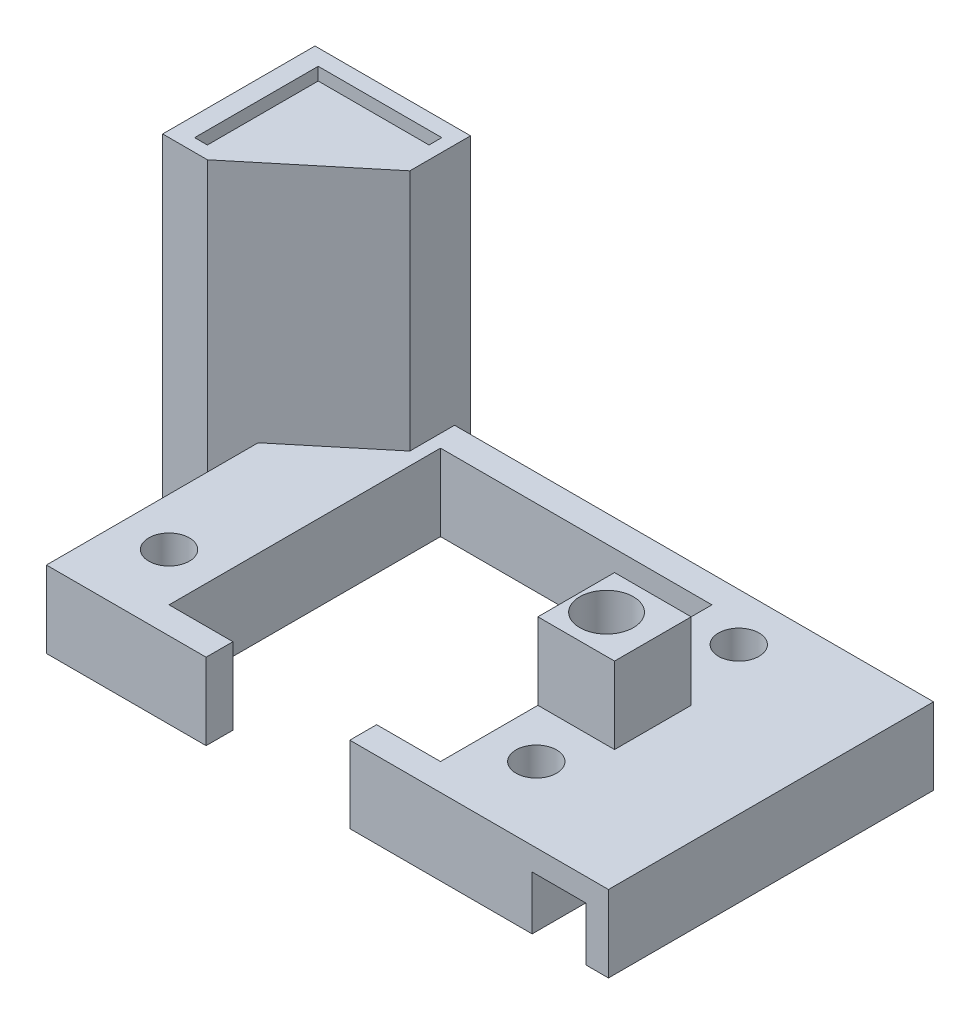
SolidWorks part; units mm, degrees
ref_plane "Front Plane" through (0, 0, 0) normal (0, 0, 1) x (1, 0, 0)
ref_plane "Top Plane" through (0, 0, 0) normal (0, 1, 0) x (1, 0, 0)
ref_plane "Right Plane" through (0, 0, 0) normal (1, 0, 0) x (0, 0, -1)
sketch "Sketch1" plane through (0, 0, 0) normal (0, 1, 0) x (1, 0, 0)
  line L1 (0, 0) -> (42.5, 0)
  line L2 (0, 0) -> (0, 42.5)
  line L3 (0, 42.5) -> (42.5, 42.5)
  line L4 (42.5, 0) -> (42.5, 42.5)
  line L5 (-15, 0) -> (57.5, 0)
  line L6 (-15, 0) -> (-15, 46.7)
  line L7 (-15, 46.7) -> (57.5, 46.7)
  line L8 (57.5, 0) -> (57.5, 46.7)
  line L9 (-15, 0) -> (10, 0)
  line L10 (-15, 0) -> (-15, -4.2)
  line L11 (-15, -4.2) -> (10, -4.2)
  line L12 (10, 0) -> (10, -4.2)
  line L13 (57.5, 0) -> (32.5, 0)
  line L14 (57.5, 0) -> (57.5, -4.2)
  line L15 (57.5, -4.2) -> (32.5, -4.2)
  line L16 (32.5, 0) -> (32.5, -4.2)
  circle A0 centre (-7.5, 7.5) radius 3.175
  circle A2 centre (50, 39.2) radius 3.175
  circle A3 centre (50, 7.5) radius 3.175
  point P11 (-7.5, 7.5)
  point P12 (-7.5, 7.5)
  point P20 (50, 35.5771)
  dimension "D5" = 7.5
  dimension "D7" = 6.35
  dimension "D1" = 42.5
  dimension "D2" = 15
  dimension "D3" = 15
  dimension "D4" = 4.2
  dimension "D6" = 7.5
  dimension "D8" = 7.5
  dimension "D9" = 7.5
  dimension "D10" = 4.2
  dimension "D11" = 10
extrude "Boss-Extrude1" add sketch "Sketch1" along normal blind 12
sketch "Sketch4" plane through (53.3, 0, 4.2) normal (0, 0, -1) x (-1, 0, 0)
  line L0 (-7.75, 8.4) -> (-4.2, 8.4) construction
  line L1 (-19.7, 0) -> (-4.2, 0)
  line L2 (-19.7, 0) -> (-19.7, 12)
  line L3 (-19.7, 12) -> (-4.2, 12)
  line L4 (-4.2, 0) -> (-4.2, 12)
  line L5 (-16.15, 0) -> (-7.75, 0)
  line L6 (-16.15, 0) -> (-16.15, 8.4)
  line L7 (-16.15, 8.4) -> (-7.75, 8.4)
  line L8 (-7.75, 0) -> (-7.75, 8.4)
  line L9 (-16.15, 8.4) -> (-19.7, 8.4) construction
  point P9 (-21.0668, -0.3569)
  point P12 (-4.2, 0)
  line M16 (-4.2, 0) -> (-4.2, 12)
  dimension "D1" = 15.5
  dimension "D2" = 12
  dimension "D3" = 8.4
extrude "Boss-Extrude2" add sketch "Sketch4" along normal up to surface (50.9 mm away) contours L1 L8 L7 L6 L2 L3 L4 M16 up to face at (21.25, 6, -46.7)
sketch "Sketch5" plane through (0, 12, 0) normal (0, 1, 0) x (1, 0, 0)
  line L0 (42.5, 0) -> (42.5, 42.5) construction
  line L1 (42.5, 27.25) -> (54.5, 27.25)
  line L2 (42.5, 27.25) -> (42.5, 15.25)
  line L3 (42.5, 15.25) -> (54.5, 15.25)
  line L4 (54.5, 27.25) -> (54.5, 15.25)
  line L5 (21.25, 42.5) -> (21.25, -4.8094) construction
  line L7 (0, 42.5) -> (42.5, 42.5) construction
  line L8 (54.5, 21.25) -> (42.5, 21.25) construction
  circle A0 centre (47.25, 21.25) radius 4.2
  point P11 (21.25, 42.5)
  point P15 (47.25, 23.778)
  point P16 (42.5, 15.4964)
  point P17 (42.5, 21.25)
  dimension "D2" = 8.4
  dimension "D1" = 26
  dimension "D3" = 12
  dimension "D4" = 12
extrude "Boss-Extrude3" add sketch "Sketch5" along normal blind 12
sketch "Sketch6" plane through (0, 0, 0) normal (0, -1, 0) x (1, 0, 0)
  line L0 (-19.35, -25.35) -> (-2, -39.7)
  line L1 (-4, -46.7) -> (-4, -44.7)
  line L2 (-4, -46.7) -> (-23.35, -46.7)
  line L3 (-23.35, -46.7) -> (-23.35, -27.35)
  line L6 (-4, -44.7) -> (-21.35, -44.7)
  line L7 (-21.35, -44.7) -> (-21.35, -27.35)
  line L8 (-21.35, -27.35) -> (-23.35, -27.35)
  line L9 (-2, -46.7) -> (-2, -39.7)
  line L10 (-26.35, -46.7) -> (-26.35, -25.35)
  line L11 (-26.35, -46.7) -> (-2, -46.7)
  line L16 (-19.35, -25.35) -> (-26.35, -25.35)
  line L18 (-26.35, -46.7) -> (-26.35, -49.2)
  line L19 (-26.35, -46.7) -> (-2, -46.7)
  line L20 (-2, -46.7) -> (-2, -49.2)
  line L21 (-26.35, -49.2) -> (-2, -49.2)
  line L24 (-15, 4.2) -> (-15, -46.7) construction
  line L26 (-15, -46.7) -> (61.05, -46.7) construction
  point P4 (-8.7381, -56.7233)
  point P5 (-2.4586, -52.8762)
  point P7 (-1.9793, -49.0716)
  point P10 (-19.35, -56.2487)
  point P12 (-2, -56.6979)
  point P14 (-2, -56.2487)
  point P16 (-19.35, -33.9237)
  point P17 (-2, -48.058)
  point P20 (-2, -49.705)
  point P25 (-2, -47.5176)
  point P29 (0, 0)
  line M15 (-15, 4.2) -> (-15, -46.7)
  line M16 (-15, -46.7) -> (61.05, -46.7)
  dimension "D1" = 19.35
  dimension "D2" = 2
  dimension "D3" = 3
  dimension "D4" = 2
  dimension "D5" = 2
  dimension "D6" = 7
  dimension "D7" = 11
  dimension "D8" = 2.5
  dimension "D9" = 2.5
extrude "Boss-Extrude8" add sketch "Sketch6" against normal blind 50 contours L9 L0 L6 L1 M16 M15 | L0 L16 L10 L11 L3 L8 L7 L6 M15 | L18 L21 L20 L2 L11 M16
equation "\"8mm hole\" = 8.4mm"
equation "\"22mm hole\"= 23mm"
equation "\"15mm hole\"= 15.8mm"
equation "\"bed height offset\"= 3mm"
equation "\"motor width\"= 42.5mm"
equation "\"D3@Sketch4\"= \"8mm hole\""
equation "\"D2@Sketch5\"= \"8mm hole\""
